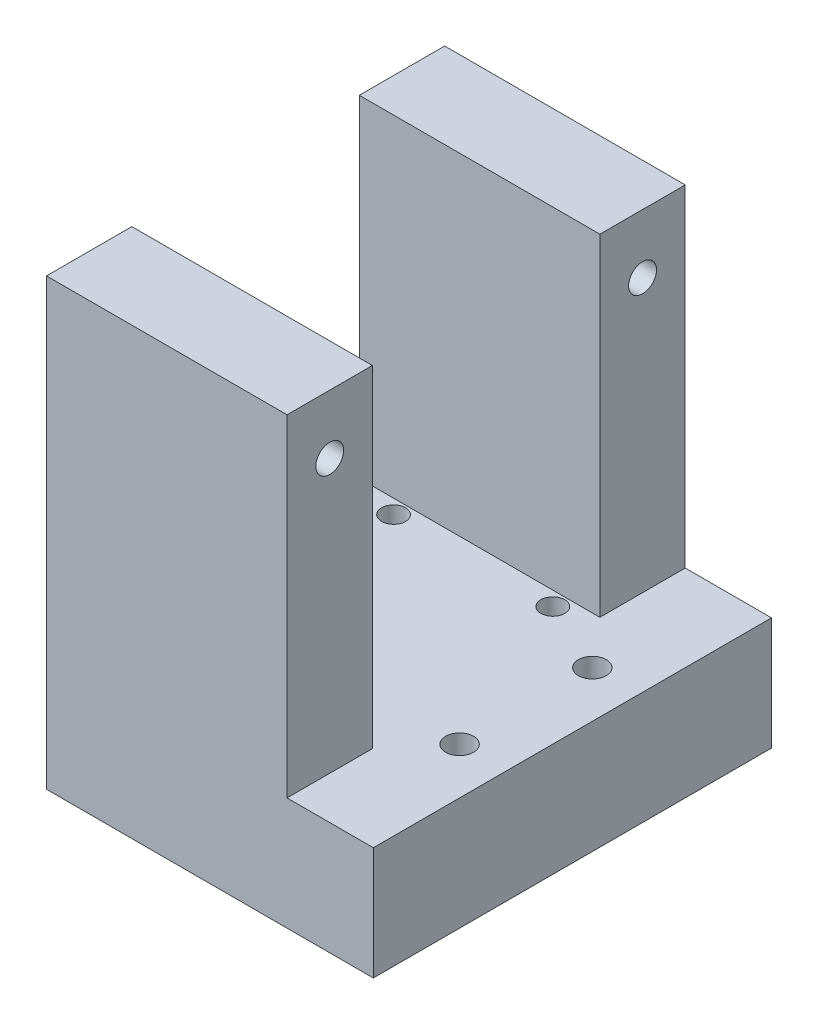
SolidWorks part; units mm, degrees
ref_plane "Alzado" through (0, 0, 0) normal (0, 0, 1) x (1, 0, 0)
ref_plane "Planta" through (0, 0, 0) normal (0, 1, 0) x (1, 0, 0)
ref_plane "Vista lateral" through (0, 0, 0) normal (1, 0, 0) x (0, 0, -1)
sketch "Croquis1" plane through (0, 0, 0) normal (0, 1, 0) x (1, 0, 0)
  line L10 (0, 0) -> (48.11, 0)
  line L11 (0, 40) -> (0, 0)
  line L15 (0, 40) -> (48.11, 40)
  line L18 (48.11, 40) -> (48.25, 40)
  line L19 (48.11, 0) -> (48.25, 0)
  line L20 (48.25, 0) -> (48.25, 20)
  line L21 (48.25, 40) -> (48.25, 20)
  circle A0 centre (7.3, 5) radius 1.8
  circle A1 centre (31.3, 5) radius 1.8
  circle A2 centre (31.3, 35) radius 1.8
  circle A3 centre (7.3, 35) radius 1.8
  circle A8 centre (42.25, 30) radius 2.1
  circle A9 centre (42.25, 10) radius 2.1
extrude "Saliente-Extruir4" add sketch "Croquis1" along normal blind 17
sketch "Croquis2" plane through (0, 17, 0) normal (0, 1, 0) x (1, 0, 0)
  line L0 (0, 40) -> (0, 50)
  line L1 (48.25, 40) -> (48.25, 50)
  line L2 (48.25, 50) -> (0, 50)
  line L3 (48.25, 0) -> (48.25, -10)
  line L4 (0, 0) -> (0, -10)
  line L5 (0, -10) -> (48.25, -10)
  line L6 (0, 40) -> (48.25, 40)
  line L7 (0, 0) -> (48.25, 0)
extrude "Saliente-Extruir5" add sketch "Croquis2" against normal blind 17
sketch "Croquis3" plane through (0, 17, 0) normal (0, 1, 0) x (1, 0, 0)
  line L0 (0, 50) -> (36.25, 50)
  line L1 (48.25, 50) -> (0, 50) construction
  line L2 (0, 50) -> (0, 37.14)
  line L3 (0, 50) -> (0, -10) construction
  line L4 (0, -10) -> (0, 2.86)
  line L5 (36.25, 50) -> (36.25, 37.14)
  line L6 (0, -10) -> (48.25, -10) construction
  line L7 (36.25, -10) -> (0, -10)
  line L8 (0, 2.86) -> (36.25, 2.86)
  line L9 (0, 37.14) -> (36.25, 37.14)
  line L10 (36.25, 2.86) -> (36.25, -10)
extrude "Saliente-Extruir6" add sketch "Croquis3" along normal blind 50
sketch "Croquis4" plane through (0, 0, 0) normal (-1, 0, 0) x (0, 0, 1)
  circle A0 centre (-43.57, 58.1) radius 2.1
  circle A1 centre (3.57, 58.1) radius 2.1
extrude "Cortar-Extruir1" cut sketch "Croquis4" against normal blind 50
sketch "Croquis5" plane through (48.25, 0, 0) normal (1, 0, 0) x (0, 0, -1)
  line L0 (50, 0) -> (-10, 0)
  line L1 (-10, 0) -> (-10, 17)
  line L2 (-10, 17) -> (50, 17)
  line L3 (50, 17) -> (50, 0)
extrude "Saliente-Extruir7" add sketch "Croquis5" along normal blind 1
